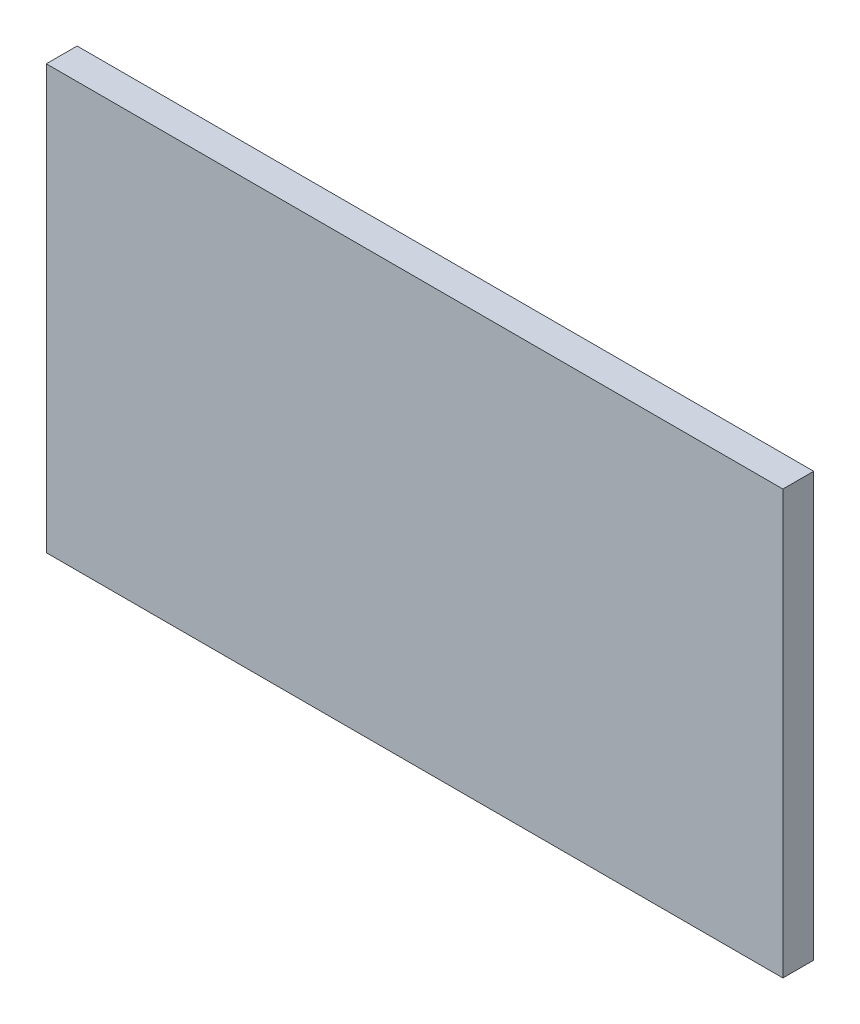
SolidWorks part; units mm, degrees
material "Custom Plastic"
ref_plane "Front Plane" through (0, 0, 0) normal (0, 0, 1) x (1, 0, 0)
ref_plane "Top Plane" through (0, 0, 0) normal (0, 1, 0) x (1, 0, 0)
ref_plane "Right Plane" through (0, 0, 0) normal (1, 0, 0) x (0, 0, -1)
sketch "Sketch1" plane through (0, 0, 0) normal (0, 0, 1) x (1, 0, 0)
  line L1 (-2462.1179, 430.2609) -> (-1004.1579, 430.2609)
  line L2 (-2462.1179, 430.2609) -> (-2462.1179, -407.9391)
  line L3 (-2462.1179, -407.9391) -> (-1004.1579, -407.9391)
  line L4 (-1004.1579, 430.2609) -> (-1004.1579, -407.9391)
  line L5 (-2462.1179, 430.2609) -> (-1004.1579, -407.9391) construction
  line L6 (-2462.1179, -407.9391) -> (-1004.1579, 430.2609) construction
  point P0 (-1733.1379, 11.1609)
  dimension "D1" = 838.2
  dimension "D2" = 1457.96
extrude "Boss-Extrude1" add sketch "Sketch1" along normal blind 60.96
